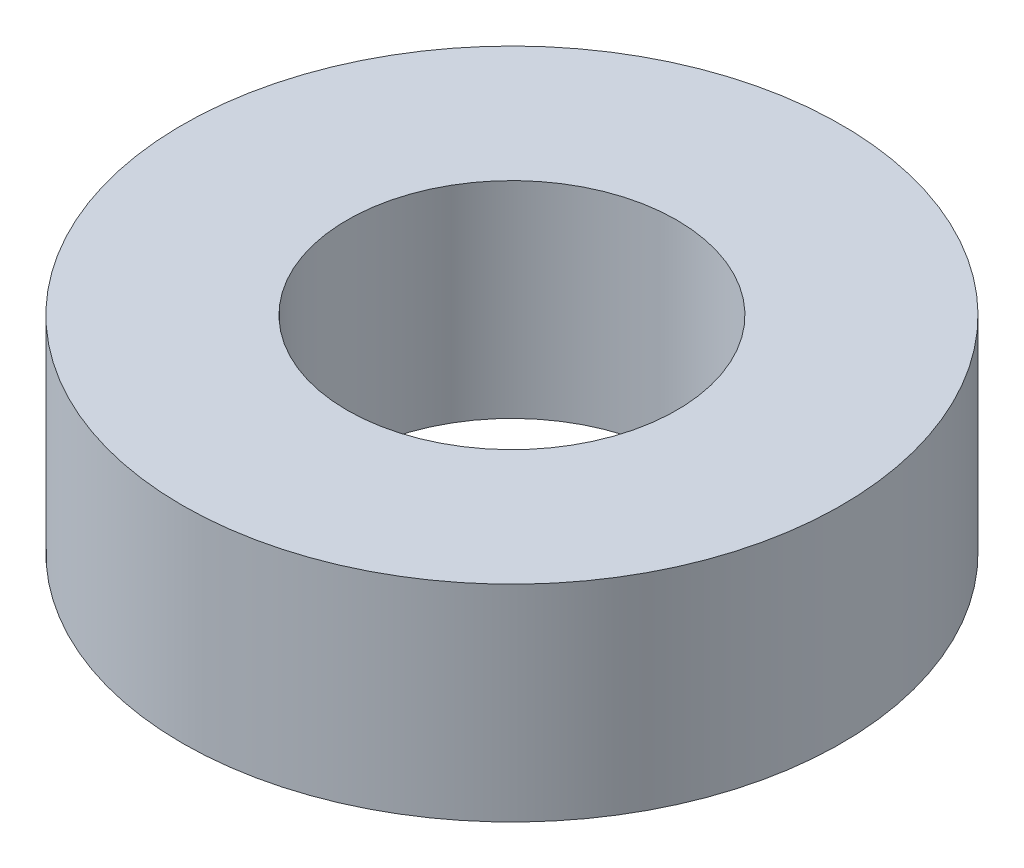
SolidWorks part; units mm, degrees
ref_plane "Front Plane" through (0, 0, 0) normal (0, 0, 1) x (1, 0, 0)
ref_plane "Top Plane" through (0, 0, 0) normal (0, 1, 0) x (1, 0, 0)
ref_plane "Right Plane" through (0, 0, 0) normal (1, 0, 0) x (0, 0, -1)
sketch "Sketch1" plane through (0, 0, 0) normal (0, 1, 0) x (1, 0, 0)
  circle A0 centre (0, 0) radius 8
  dimension "D1" = 16
extrude "Boss-Extrude1" add sketch "Sketch1" along normal blind 5
sketch "Sketch2" plane through (0, 5, 0) normal (0, 1, 0) x (1, 0, 0)
  circle A0 centre (0, 0) radius 4
  dimension "D1" = 8
extrude "Cut-Extrude1" cut sketch "Sketch2" against normal up to surface (5 mm away) up to face at (0, 0, 8)
